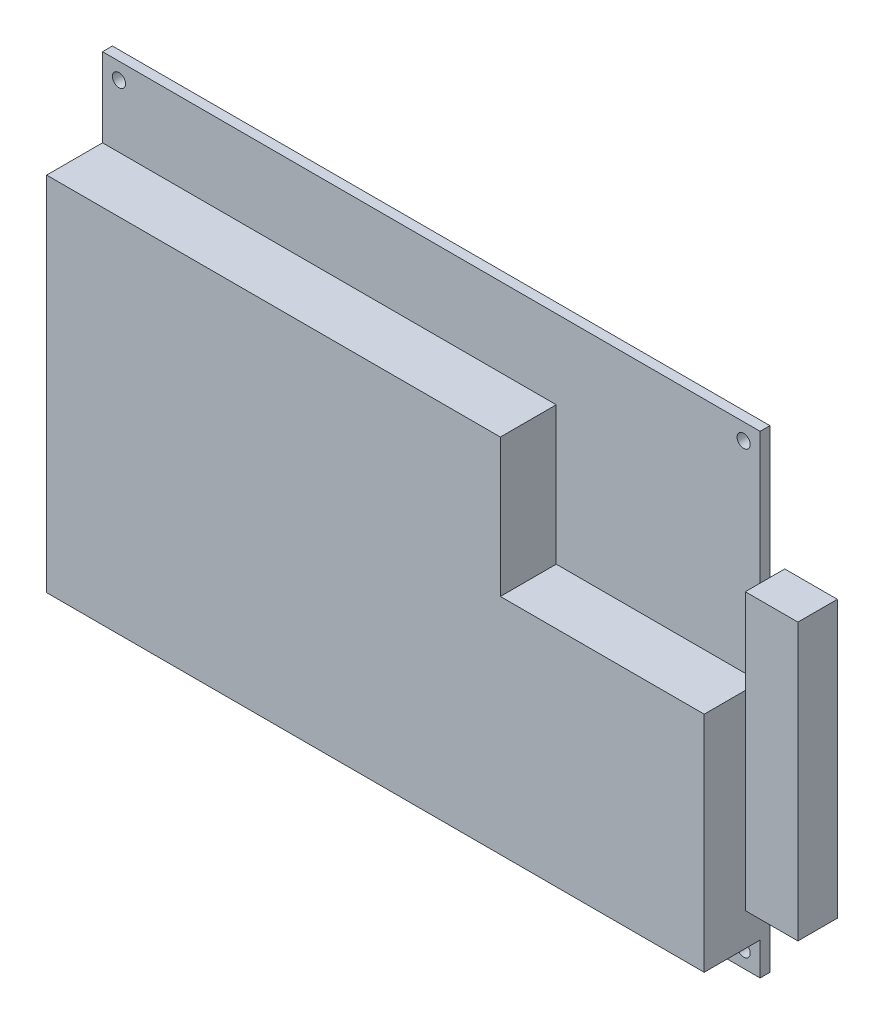
SolidWorks part; units mm, degrees
ref_plane "Plan de face" through (0, 0, 0) normal (0, 0, 1) x (1, 0, 0)
ref_plane "Plan de dessus" through (0, 0, 0) normal (0, 1, 0) x (1, 0, 0)
ref_plane "Plan de droite" through (0, 0, 0) normal (1, 0, 0) x (0, 0, -1)
sketch "Main" plane through (0, 0, 0) normal (0, 0, 1) x (1, 0, 0)
  line L1 (100, 72) -> (0, 72)
  line L2 (100, 72) -> (100, 0)
  line L3 (100, 0) -> (0, 0)
  line L4 (0, 72) -> (0, 0)
  circle A0 centre (2.5, 69.5) radius 1
  circle A1 centre (2.5, 2.5) radius 1
  circle A2 centre (97.5, 69.5) radius 1
  circle A3 centre (97.5, 2.5) radius 1
  dimension "D3" = 2
  dimension "D1" = 100
  dimension "D2" = 72
  dimension "D4" = 2.5
  dimension "D5" = 2.5
  dimension "D6" = 2.5
  dimension "D7" = 2.5
extrude "Main-Extrusion" add sketch "Main" along normal blind 1.5
sketch "Bottom-Hole-Sketch" plane through (0, 0, 1.5) normal (0, 0, 1) x (1, 0, 0)
  line L0 (0, 60) -> (69, 60)
  line L1 (0, 72) -> (0, 0) construction
  line L3 (69, 60) -> (69, 39)
  line L4 (69, 5) -> (0, 5)
  line L5 (0, 5) -> (0, 60)
  line L6 (100, 72) -> (0, 72) construction
  line L7 (69, 39) -> (100, 39)
  line L8 (100, 0) -> (100, 72) construction
  line L9 (100, 39) -> (100, 5)
  line L10 (100, 5) -> (69, 5)
  dimension "D1" = 12
  dimension "D2" = 55
  dimension "D3" = 69
  dimension "D4" = 21
extrude "Bottom-Hole" add sketch "Bottom-Hole-Sketch" along normal blind 8.5
sketch "Ide-Connector-Sketch" plane through (100, 0, 0) normal (1, 0, 0) x (0, 0, -1)
  line L1 (-3.75, 52) -> (2.25, 52)
  line L2 (-3.75, 52) -> (-3.75, 10)
  line L3 (-3.75, 10) -> (2.25, 10)
  line L4 (2.25, 52) -> (2.25, 10)
  line L5 (-1.5, 72) -> (0, 72) construction
  line L7 (-10, 5) -> (-1.5, 5) construction
  point P4 (2.25, 12.5417)
  point P8 (-0.75, 72)
  point P9 (0, 0)
  point P10 (-0.75, 52)
  dimension "D1" = 6
  dimension "D2" = 5
  dimension "D3" = 42
extrude "Ide-Connector-Extrusion" add sketch "Ide-Connector-Sketch" along normal blind 8
